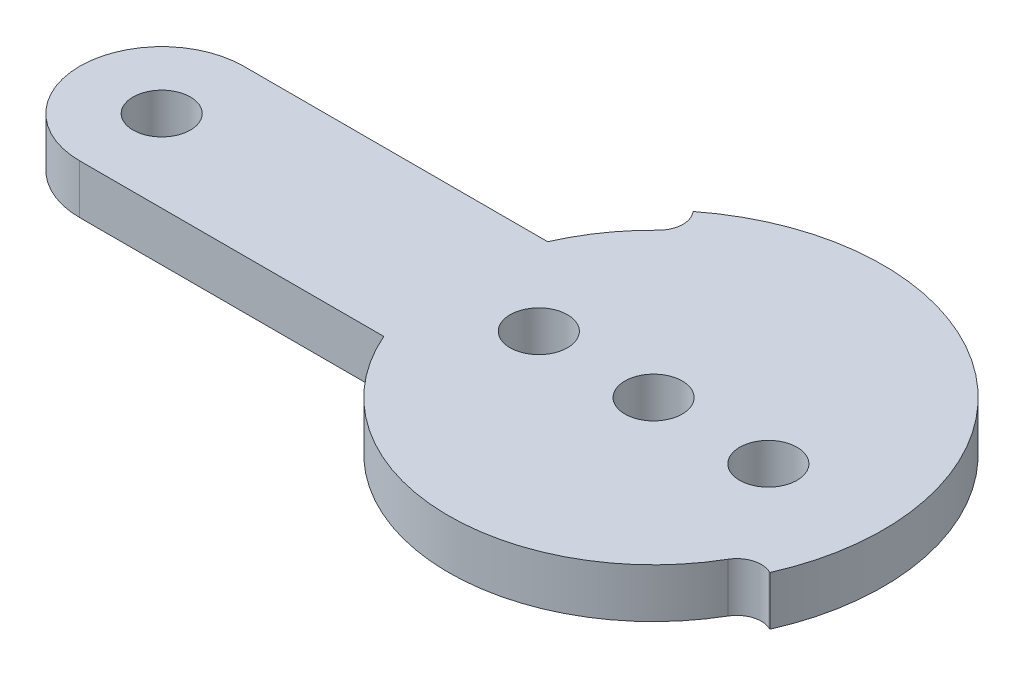
SolidWorks part; units mm, degrees
material "PET"
ref_plane "Спереди" through (0, 0, 0) normal (0, 0, 1) x (1, 0, 0)
ref_plane "Сверху" through (0, 0, 0) normal (0, 1, 0) x (1, 0, 0)
ref_plane "Справа" through (0, 0, 0) normal (1, 0, 0) x (0, 0, -1)
sketch "Эскиз1" plane through (0, 0, 0) normal (0, 1, 0) x (1, 0, 0)
  line L0 (0, 0) -> (-30, 0) construction
  line L1 (-30, 5) -> (-11.4564, 5)
  line L2 (-30, -5) -> (-11.4564, -5)
  line L4 (12.716, -5.6615) -> (12.7896, -5.6943)
  line L5 (-8.5696, 10.9686) -> (-8.6193, 11.0322)
  arc A0 (12.7896, -5.6943) -> (-8.6193, 11.0322) centre (0, 0) ccw
  arc A1 (-11.4564, -5) -> (10.8088, -6.2784) centre (0, 0) ccw
  arc A2 (-30, 5) -> (-30, -5) centre (-30, 0) ccw
  circle A3 centre (-30, 0) radius 1.75
  arc A4 (-8.7068, 8.9689) -> (-11.4564, 5) centre (0, 0) ccw
  arc A5 (10.8088, -6.2784) -> (12.716, -5.6615) centre (12.1059, -7.0319) cw
  arc A6 (-8.5696, 10.9686) -> (-8.7068, 8.9689) centre (-9.7517, 10.0452) cw
  point P13 (0, 0)
  point P16 (0, 0)
  point P18 (-7.6958, 9.8501)
  dimension "D1" = 28
  dimension "D2" = 25
  dimension "D3" = 10
  dimension "D5" = 3.5
  dimension "D6" = 1.5
  dimension "D7" = 1.5
  dimension "D4" = 30
extrude "Бобышка-Вытянуть1" add sketch "Эскиз1" along normal blind 3
sketch "Эскиз2" plane through (0, 0, 0) normal (0, -1, 0) x (1, 0, 0)
  circle A0 centre (0, 0) radius 6
  dimension "D1" = 12
extrude "Бобышка-Вытянуть2" add sketch "Эскиз2" along normal blind 3
sketch "Эскиз3" plane through (0, -3, 0) normal (0, -1, 0) x (1, 0, 0)
  circle A0 centre (0, 0) radius 1.75
  circle A1 centre (-7, 0) radius 1.75
  circle A2 centre (7, 0) radius 1.75
  dimension "D1" = 3.5
  dimension "D2" = 3.5
  dimension "D3" = 3.5
  dimension "D4" = 7
  dimension "D5" = 7
extrude "Вырез-Вытянуть1" cut sketch "Эскиз3" against normal through all
